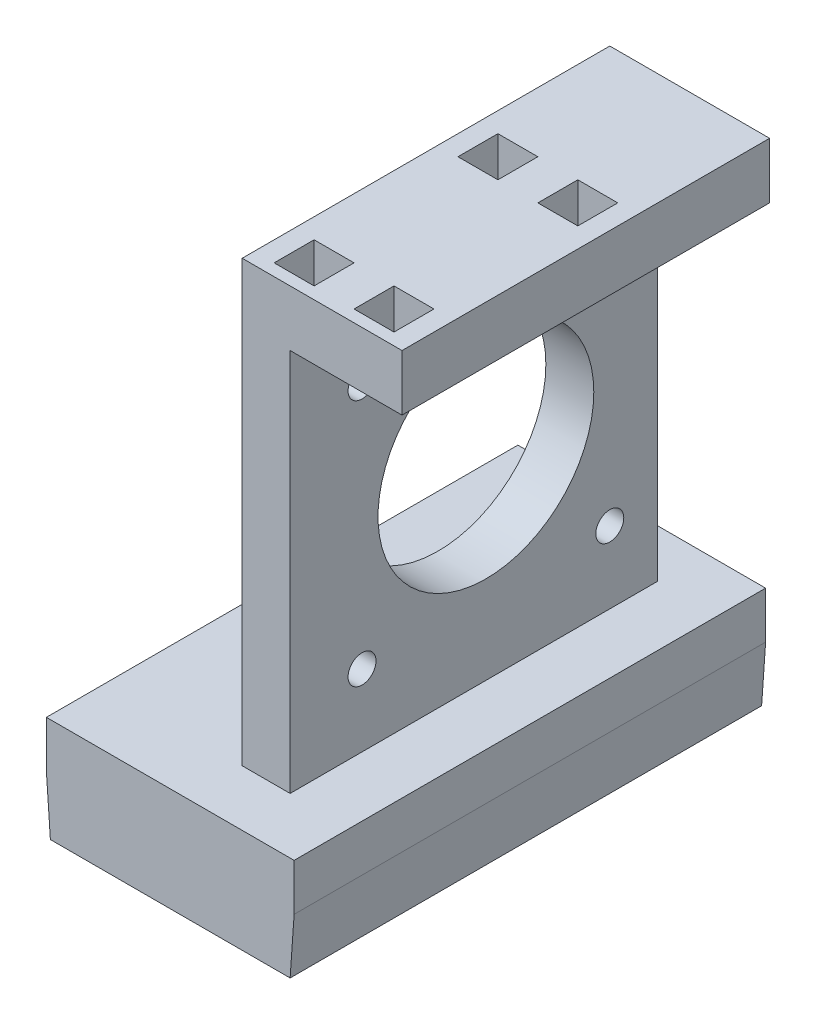
SolidWorks part; units mm, degrees
ref_plane "Front Plane" through (0, 0, 0) normal (0, 0, 1) x (1, 0, 0)
ref_plane "Top Plane" through (0, 0, 0) normal (0, 1, 0) x (1, 0, 0)
ref_plane "Right Plane" through (0, 0, 0) normal (1, 0, 0) x (0, 0, -1)
sketch "Sketch1" plane through (0, 0, 0) normal (0, 1, 0) x (1, 0, 0)
  line L0 (-23, 32) -> (-23, 22)
  line L1 (0, 0) -> (-26, 0)
  line L2 (0, 0) -> (0, 53)
  line L3 (0, 53) -> (-26, 53)
  line L4 (-26, 0) -> (-26, 53)
  line L5 (-23, 48) -> (-3, 48)
  line L6 (-23, 48) -> (-23, 38)
  line L7 (-23, 38) -> (-3, 38)
  line L8 (-3, 48) -> (-3, 38)
  line L9 (-23, 32) -> (-3, 32)
  line L10 (-3, 32) -> (-3, 22)
  line L11 (-23, 22) -> (-3, 22)
  line L12 (-23, 16) -> (-23, 6)
  line L13 (-23, 16) -> (-3, 16)
  line L14 (-3, 16) -> (-3, 6)
  line L15 (-23, 6) -> (-3, 6)
  point P9 (-13, 48)
  point P10 (-13, 53)
  dimension "D1" = 26
  dimension "D2" = 53
  dimension "D3" = 20
  dimension "D4" = 10
  dimension "D5" = 5
  dimension "D6" = 3
extrude "Boss-Extrude1" add sketch "Sketch1" along normal blind 5
sketch "Sketch2" plane through (0, 5, 0) normal (0, 1, 0) x (1, 0, 0)
  line L17 (-26, 53) -> (0, 53)
  line L18 (-26, 53) -> (-26, 0)
  line L19 (-26, 0) -> (0, 0)
  line L20 (0, 53) -> (0, 0)
  line L21 (-28.5, 56) -> (2.5, 56)
  line L22 (-28.5, 56) -> (-28.5, -3)
  line L23 (-28.5, -3) -> (2.5, -3)
  line L24 (2.5, 56) -> (2.5, -3)
  dimension "D1" = 3
  dimension "D2" = 2.5
  dimension "D3" = 2.5
  dimension "D4" = 3
extrude "Boss-Extrude2" add sketch "Sketch2" against normal blind 10
sketch "Sketch3" plane through (0, 5, 0) normal (0, 1, 0) x (1, 0, 0)
  line L1 (-28.5, 56) -> (2.5, 56)
  line L2 (-28.5, 56) -> (-28.5, -3)
  line L3 (-28.5, -3) -> (2.5, -3)
  line L4 (2.5, 56) -> (2.5, -3)
extrude "Boss-Extrude3" add sketch "Sketch3" along normal blind 3
sketch "Sketch4" plane through (0, 8, 0) normal (0, 1, 0) x (1, 0, 0)
  line L1 (-5, 50) -> (-11, 50)
  line L2 (-5, 50) -> (-5, 4)
  line L3 (-5, 4) -> (-11, 4)
  line L4 (-11, 50) -> (-11, 4)
  line L6 (-3, 38) -> (-3, 48) construction
  line L8 (-28.5, -3) -> (2.5, -3) construction
  dimension "D1" = 6
  dimension "D2" = 2
  dimension "D3" = 46
  dimension "D4" = 7
extrude "Boss-Extrude4" add sketch "Sketch4" along normal blind 55
sketch "Sketch5" plane through (-5, 0, 0) normal (1, 0, 0) x (0, 0, -1)
  line L0 (4, 8) -> (50, 8) construction
  line L1 (50, 63) -> (50, 8) construction
  line L2 (13, 48) -> (44, 17) construction
  line L3 (44, 48) -> (13, 17) construction
  circle A0 centre (44, 17) radius 1.75
  circle A1 centre (13, 17) radius 1.75
  circle A2 centre (13, 48) radius 1.75
  circle A3 centre (44, 48) radius 1.75
  circle A4 centre (28.5, 32.5) radius 13.5
  dimension "D2" = 6
  dimension "D3" = 3.5
  dimension "D6" = 27
  dimension "D1" = 9
  dimension "D4" = 2
  dimension "D5" = 2
extrude "Cut-Extrude1" cut sketch "Sketch5" against normal through all
chamfer "Chamfer1" distance 0.5 angle 86 2 edges at (2.5, -5, -26.5) (-28.5, -5, -26.5)
sketch "Sketch6" plane through (-5, 0, 0) normal (1, 0, 0) x (0, 0, -1)
  line L0 (4, 63) -> (4, 8) construction
  line L1 (50, 63) -> (4, 63)
  line L2 (50, 63) -> (50, 56)
  line L3 (50, 56) -> (4, 56)
  line L4 (4, 63) -> (4, 56)
  line L5 (50, 63) -> (50, 8) construction
  dimension "D1" = 7
extrude "Boss-Extrude5" add sketch "Sketch6" along normal blind 14
sketch "Sketch7" plane through (0, 63, 0) normal (0, 1, 0) x (1, 0, 0)
  line L0 (-11, 50) -> (-11, 4) construction
  line L1 (-8.5, 33.5) -> (-3.5, 33.5)
  line L2 (-8.5, 33.5) -> (-8.5, 28.5)
  line L3 (-8.5, 28.5) -> (-3.5, 28.5)
  line L4 (-3.5, 33.5) -> (-3.5, 28.5)
  line L5 (1.5, 33.5) -> (6.5, 33.5)
  line L6 (1.5, 33.5) -> (1.5, 28.5)
  line L7 (1.5, 28.5) -> (6.5, 28.5)
  line L8 (6.5, 33.5) -> (6.5, 28.5)
  line L9 (-8.5, 10.5) -> (-3.5, 10.5)
  line L10 (-8.5, 10.5) -> (-8.5, 5.5)
  line L11 (-8.5, 5.5) -> (-3.5, 5.5)
  line L12 (-3.5, 10.5) -> (-3.5, 5.5)
  line L13 (1.5, 10.5) -> (6.5, 10.5)
  line L14 (1.5, 10.5) -> (1.5, 5.5)
  line L15 (1.5, 5.5) -> (6.5, 5.5)
  line L16 (6.5, 10.5) -> (6.5, 5.5)
  line L17 (-11, 4) -> (9, 4) construction
  point P18 (-6, 10.5)
  point P19 (-6, 33.5)
  point P20 (4, 33.5)
  point P21 (4, 10.5)
  point P22 (-3.5, 31)
  point P23 (1.5, 31)
  point P24 (-3.5, 8)
  point P25 (1.5, 8)
  dimension "D1" = 5
  dimension "D2" = 5
  dimension "D3" = 2.5
  dimension "D4" = 1.5
  dimension "D5" = 23
extrude "Cut-Extrude2" cut sketch "Sketch7" against normal blind 5
